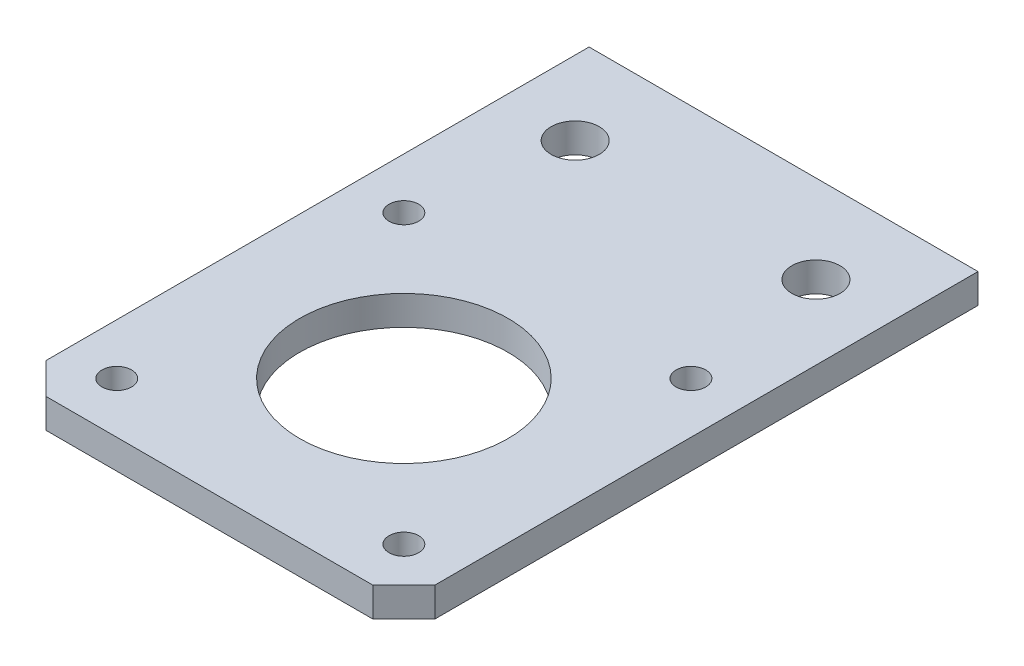
SolidWorks part; units mm, degrees
material "6061-T6 (SS)"
ref_plane "Front Plane" through (0, 0, 0) normal (0, 0, 1) x (1, 0, 0)
ref_plane "Top Plane" through (0, 0, 0) normal (0, 1, 0) x (1, 0, 0)
ref_plane "Right Plane" through (0, 0, 0) normal (1, 0, 0) x (0, 0, -1)
sketch "Sketch1" plane through (0, 0, 0) normal (0, 1, 0) x (1, 0, 0)
  line L0 (-21, -17.645) -> (-21, 17.645)
  line L1 (-17.645, 21) -> (17.645, 21)
  line L2 (21, -17.645) -> (21, 17.645)
  line L3 (-21, 17.645) -> (-17.645, 21)
  line L4 (15.5, 15.5) -> (-15.5, 15.5) construction
  line L5 (15.5, 15.5) -> (15.5, -15.5) construction
  line L6 (15.5, -15.5) -> (-15.5, -15.5) construction
  line L7 (-15.5, 15.5) -> (-15.5, -15.5) construction
  line L8 (15.5, -15.5) -> (-15.5, 15.5) construction
  line L9 (21, 17.645) -> (17.645, 21)
  line L10 (15.5, 15.5) -> (-15.5, -15.5) construction
  line L11 (0, 0) -> (-21, 0) construction
  line L12 (21, -17.645) -> (17.645, -21)
  line L13 (-17.645, -21) -> (17.645, -21)
  line L14 (-21, -17.645) -> (-17.645, -21)
  line L15 (0, 0) -> (0, 21) construction
  line L16 (21, 17.645) -> (21, 41)
  line L17 (21, 41) -> (-21, 41)
  line L18 (-21, 41) -> (-21, 17.645)
  line L19 (-21, 31.5) -> (21, 31.5) construction
  circle A0 centre (0, 0) radius 11.25
  circle A1 centre (-15.5, -15.5) radius 1.6
  circle A2 centre (-15.5, 15.5) radius 1.6
  circle A3 centre (15.5, 15.5) radius 1.6
  circle A4 centre (15.5, -15.5) radius 1.6
  circle A5 centre (13, 31.5) radius 2.6
  circle A6 centre (-13, 31.5) radius 2.6
  dimension "D2" = 3.2
  dimension "D7" = 22.5
  dimension "D9" = 5.2
  dimension "D10" = 5.2
  dimension "D11" = 8
  dimension "D1" = 31
  dimension "D3" = 42
  dimension "D4" = 42
  dimension "D5" = 3.355
  dimension "D6" = 135
  dimension "D8" = 9.5
  dimension "D12" = 31.5
extrude "Boss-Extrude1" add sketch "Sketch1" along normal blind 3.175 contours L17 L18 L3 L1 L9 L16 A6 A5 | L0 L14 L13 L12 L2 L9 L1 L3 A4 A3 A2 A1 A0
